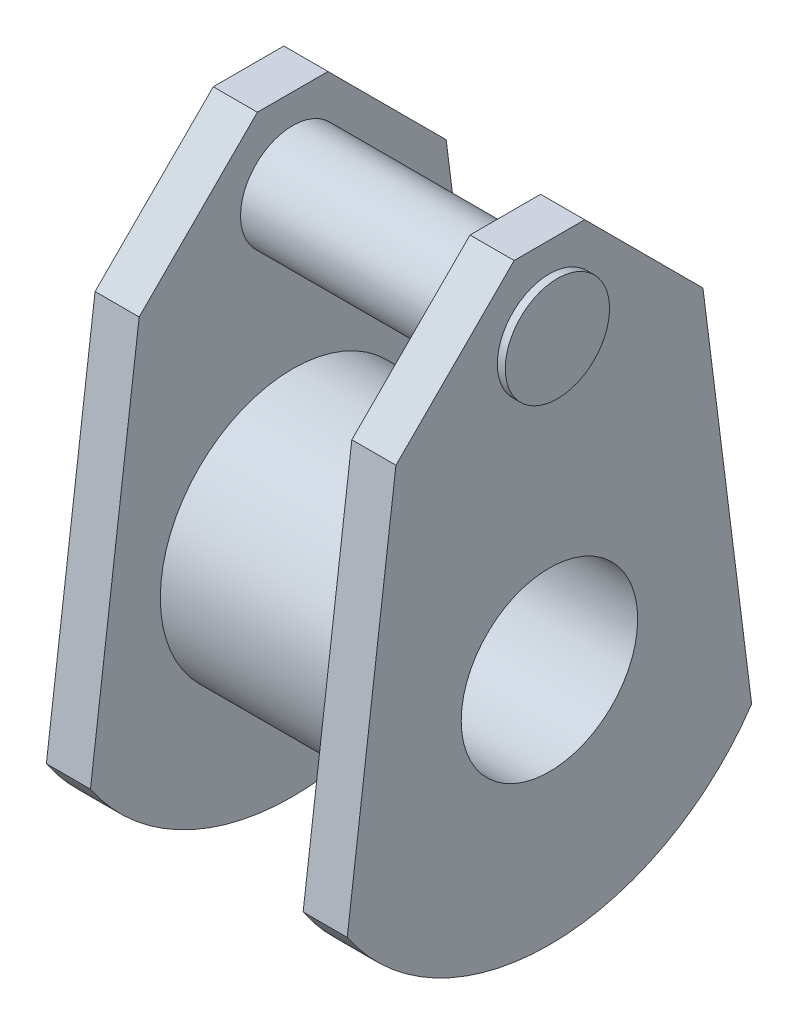
SolidWorks part; units mm, degrees
ref_plane "Ön Düzlem" through (0, 0, 0) normal (0, 0, 1) x (1, 0, 0)
ref_plane "Üst Düzlem" through (0, 0, 0) normal (0, 1, 0) x (1, 0, 0)
ref_plane "Sağ Düzlem" through (0, 0, 0) normal (1, 0, 0) x (0, 0, -1)
sketch "Çizim2" plane through (0, 0, 0) normal (1, 0, 0) x (0, 0, -1)
  circle A0 centre (0, 0) radius 10
  circle A1 centre (0, 0) radius 15
extrude "Yükseklik-Ekstrüzyon1" add sketch "Çizim2" along normal mid plane 24.1 contours A1 | A0
sketch "Çizim3" plane through (12.05, 0, 0) normal (1, 0, 0) x (0, 0, -1)
  line L0 (0, -1053.9813) -> (0, -26.9907) construction
  line L1 (-4, 42.1769) -> (4, 42.1769)
  line L2 (-4, 42.1769) -> (-17.3956, 28.7813)
  line L3 (-17.3956, 28.7813) -> (-22.9145, -14.8053)
  line L4 (17.3956, 28.7813) -> (22.9145, -14.8053)
  line L5 (4, 42.1769) -> (17.3956, 28.7813)
  line L6 (0, 42.1769) -> (0, 1042.9767) construction
  arc A0 (-22.9145, -14.8053) -> (22.9145, -14.8053) centre (0, 0.6473) ccw
  circle A1 centre (0, 0) radius 10 construction
  circle A2 centre (0, 0) radius 10
  point P6 (0, 42.1769)
extrude "Yükseklik-Ekstrüzyon2" add sketch "Çizim3" along normal blind 5
sketch "Çizim4" plane through (-12.05, 0, 0) normal (-1, 0, 0) x (0, 0, 1)
  line L0 (-4, 42.1769) -> (4, 42.1769) construction
  line L1 (4, 42.1769) -> (17.3956, 28.7813) construction
  line L2 (17.3956, 28.7813) -> (22.9145, -14.8053) construction
  line L3 (-22.9145, -14.8053) -> (-17.3956, 28.7813) construction
  line L4 (-17.3956, 28.7813) -> (-4, 42.1769) construction
  line L5 (-4, 42.1769) -> (4, 42.1769)
  line L6 (4, 42.1769) -> (17.3956, 28.7813)
  line L7 (17.3956, 28.7813) -> (22.9145, -14.8053)
  line L8 (-22.9145, -14.8053) -> (-17.3956, 28.7813)
  line L9 (-17.3956, 28.7813) -> (-4, 42.1769)
  arc A0 (-22.9145, -14.8053) -> (22.9145, -14.8053) centre (0, 0.6473) ccw construction
  circle A1 centre (0, 0) radius 15
  circle A2 centre (0, 0) radius 15
  arc A3 (-22.9145, -14.8053) -> (22.9145, -14.8053) centre (0, 0.6473) ccw
  dimension "D1" = 0
extrude "Yükseklik-Ekstrüzyon3" add sketch "Çizim4" along normal blind 5 separate body
sketch "Çizim5" plane through (-17.05, 0, 0) normal (-1, 0, 0) x (0, 0, 1)
  line L0 (0, 42.1769) -> (0, 32.4152) construction
  line L1 (4, 42.1769) -> (-4, 42.1769) construction
  circle A0 centre (0, 32.9574) radius 5.907
sketch "Çizim7" plane through (-12.05, 0, 0) normal (-1, 0, 0) x (0, 0, 1)
  circle A0 centre (0, 0) radius 15
  circle A1 centre (0, 0) radius 10
extrude "Yükseklik-Ekstrüzyon4" add sketch "Çizim7" along normal blind 5
extrude "Yükseklik-Ekstrüzyon5" add sketch "Çizim5" along normal blind 1 and the other way blind 35 contours A0
sketch "Çizim8" plane through (0, 0, 0) normal (0, 0, 1) x (1, 0, 0)
  line L0 (-12.05, 14.9423) -> (12.05, 15)
  line L1 (-12.05, 14.9423) -> (-11.9835, -12.8344)
  line L2 (12.05, 15) -> (12.1165, -12.7768)
  line L3 (-11.9835, -12.8344) -> (12.1165, -12.7768)
  line L4 (-12.05, -14.8053) -> (-12.05, 28.7813) construction
ref_plane "Düzlem1" through (0, 0, 68.7606) normal (0, 0, 1) x (1, 0, 0)
sketch "Çizim9" plane through (0, 0, 68.7606) normal (0, 0, 1) x (1, 0, 0)
  line L0 (-12.05, 14.9423) -> (12.05, 15)
  line L1 (-12.05, 14.9423) -> (-11.9793, -14.6186)
  line L2 (12.05, 15) -> (12.1207, -14.561)
  line L3 (-11.9793, -14.6186) -> (12.1207, -14.561)
